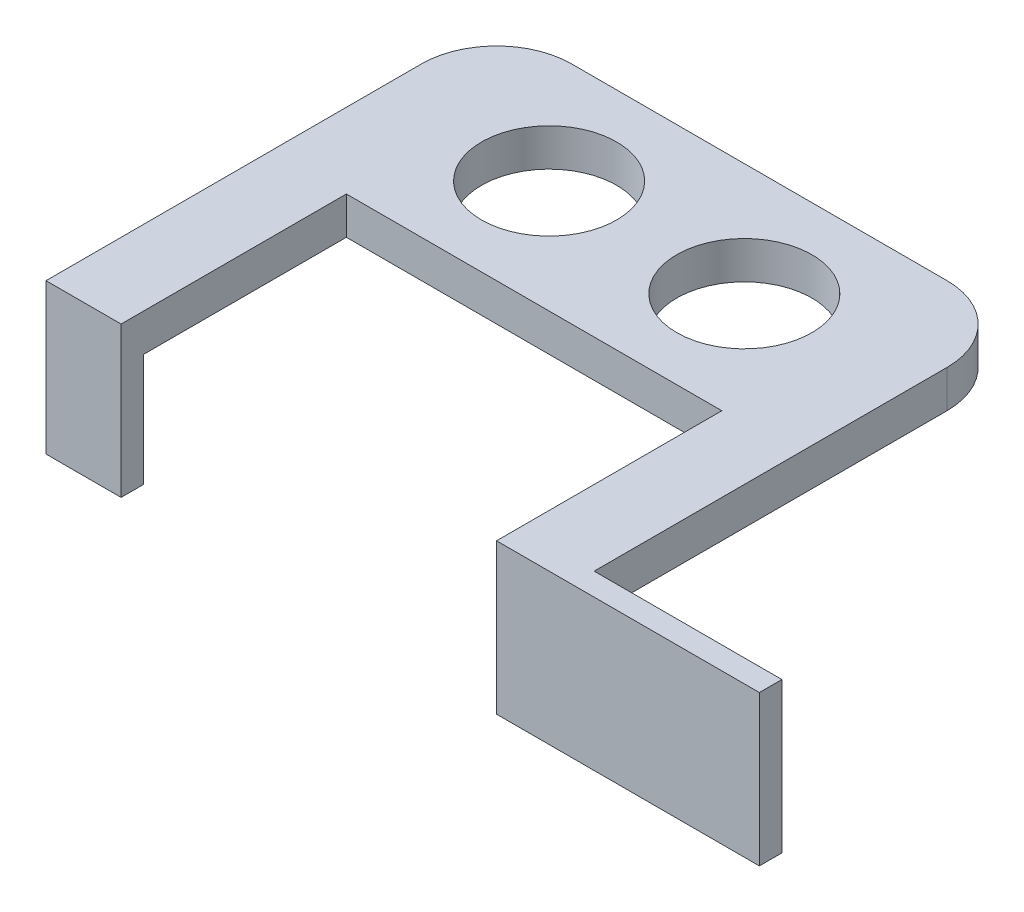
SolidWorks part; units mm, degrees
ref_plane "Plan de face" through (0, 0, 0) normal (0, 0, 1) x (1, 0, 0)
ref_plane "Plan de dessus" through (0, 0, 0) normal (0, 1, 0) x (1, 0, 0)
ref_plane "Plan de droite" through (0, 0, 0) normal (1, 0, 0) x (0, 0, -1)
sketch "Esquisse3" plane through (0, 0, 0) normal (0, 1, 0) x (1, 0, 0)
  line L0 (-42.0499, -18.2951) -> (-42.0499, 31.7049)
  line L1 (-32.0499, 41.7049) -> (17.9501, 41.7049)
  line L2 (27.9501, 31.7049) -> (27.9501, -15.2951)
  line L3 (27.9501, -15.2951) -> (52.9501, -15.2951)
  line L4 (52.9501, -15.2951) -> (52.9501, -18.2951)
  line L5 (52.9501, -18.2951) -> (17.9501, -18.2951)
  line L6 (17.9501, -18.2951) -> (17.9501, 11.7049)
  line L7 (17.9501, 11.7049) -> (-32.0499, 11.7049)
  line L8 (-32.0499, 11.7049) -> (-32.0499, -18.2951)
  line L9 (-32.0499, -18.2951) -> (-42.0499, -18.2951)
  circle A0 centre (-20.0499, 26.7049) radius 9
  circle A1 centre (5.9501, 26.7049) radius 9
  arc A2 (17.9501, 41.7049) -> (27.9501, 31.7049) centre (17.9501, 31.7049) cw
  arc A3 (-42.0499, 31.7049) -> (-32.0499, 41.7049) centre (-32.0499, 31.7049) cw
  point P12 (-7.0499, 41.7049)
  point P18 (27.9501, 41.7049)
  point P21 (-42.0499, 41.7049)
  dimension "D8" = 18
  dimension "D10" = 18
  dimension "D14" = 10
  dimension "D1" = 30
  dimension "D2" = 30
  dimension "D3" = 70
  dimension "D4" = 10
  dimension "D5" = 10
  dimension "D6" = 25
  dimension "D7" = 3
  dimension "D9" = 13
  dimension "D11" = 13
  dimension "D12" = 26
  dimension "D13" = 15
extrude "Boss.-Extru.1" add sketch "Esquisse3" along normal blind 5
sketch "Esquisse4" plane through (0, 5, 0) normal (0, 1, 0) x (1, 0, 0)
  line L0 (-32.0499, -18.2951) -> (-32.0499, 11.7049) construction
  line L1 (-42.0499, -18.2951) -> (-32.0499, -18.2951)
  line L2 (-42.0499, -18.2951) -> (-42.0499, -15.2951)
  line L3 (-42.0499, -15.2951) -> (-32.0499, -15.2951)
  line L4 (-32.0499, -18.2951) -> (-32.0499, -15.2951)
  line L6 (17.9501, -18.2951) -> (52.9501, -18.2951)
  line L7 (17.9501, -18.2951) -> (17.9501, -15.2951)
  line L8 (17.9501, -15.2951) -> (52.9501, -15.2951)
  line L9 (52.9501, -18.2951) -> (52.9501, -15.2951)
  dimension "D1" = 3
extrude "Boss.-Extru.2" add sketch "Esquisse4" against normal blind 20
